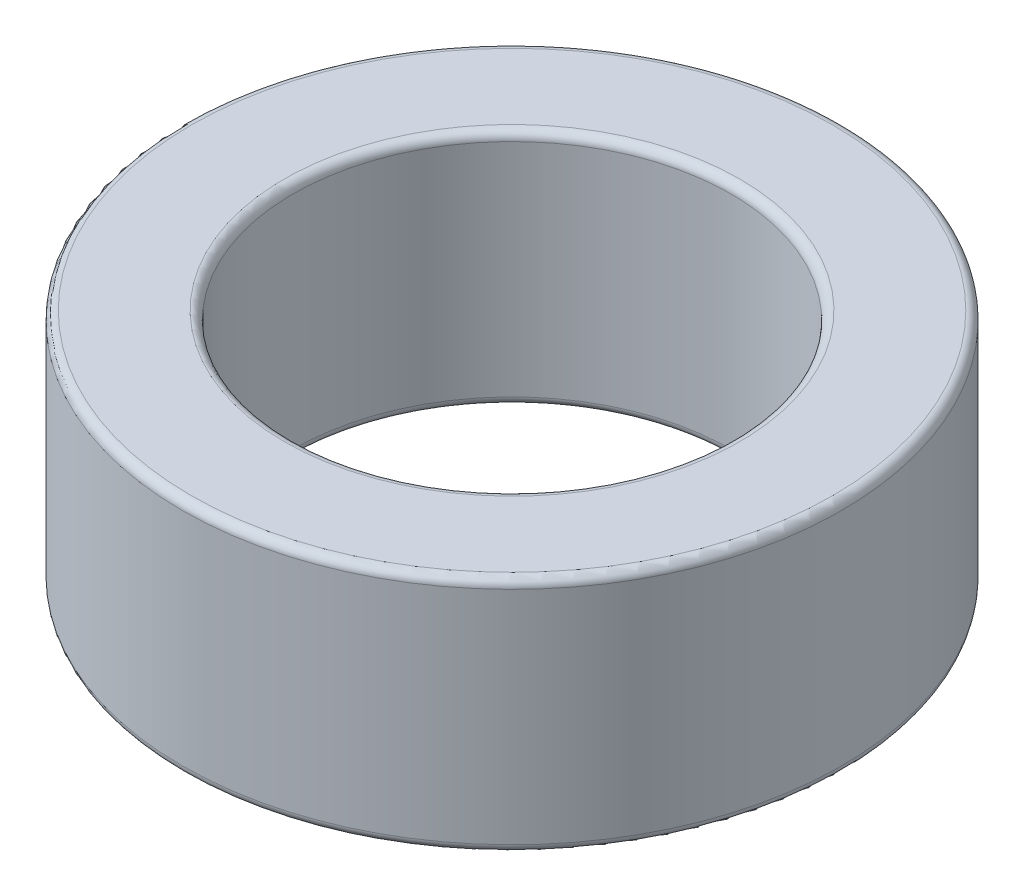
SolidWorks part; units mm, degrees
material "Полиамид ПА-6Б ТУ 6-05-988-93"
ref_plane "Спереди" through (0, 0, 0) normal (0, 0, 1) x (1, 0, 0)
ref_plane "Сверху" through (0, 0, 0) normal (0, 1, 0) x (1, 0, 0)
ref_plane "Справа" through (0, 0, 0) normal (1, 0, 0) x (0, 0, -1)
sketch "Эскиз1" plane through (0, 0, 0) normal (0, 1, 0) x (1, 0, 0)
  circle A0 centre (0, 0) radius 3.8
  circle A1 centre (0, 0) radius 2.525
  dimension "D1" = 7.6
  dimension "D2" = 5.05
extrude "Бобышка-Вытянуть1" add sketch "Эскиз1" along normal blind 2.75
fillet "Скругление1" radius 0.1 4 edges at (0, 0, 2.525) (0, 0, 3.8) (0, 2.75, 2.525) (0, 2.75, 3.8)
